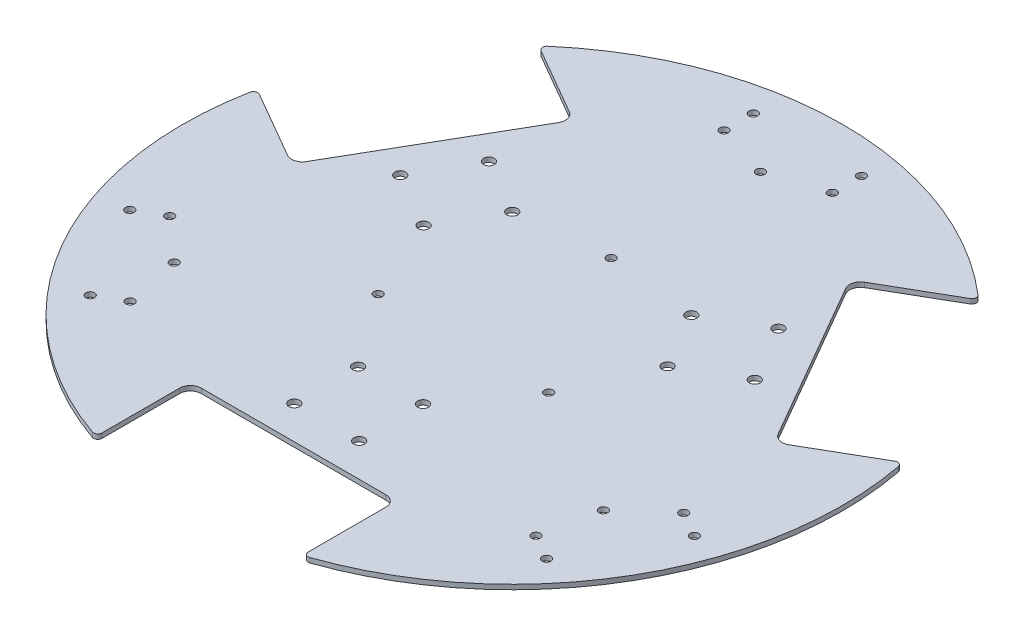
SolidWorks part; units mm, degrees
material "1060 Alloy"
ref_plane "Front Plane" through (0, 0, 0) normal (0, 0, 1) x (1, 0, 0)
ref_plane "Top Plane" through (0, 0, 0) normal (0, 1, 0) x (1, 0, 0)
ref_plane "Right Plane" through (0, 0, 0) normal (1, 0, 0) x (0, 0, -1)
sketch "Sketch1" plane through (0, 0, 0) normal (0, 1, 0) x (1, 0, 0)
  line L0 (0, -209.1984) -> (0, 195.424) construction
  line L1 (-47.65, -142.0744) -> (-47.65, -106.2645)
  line L2 (-42.65, -101.2645) -> (42.65, -101.2645)
  line L3 (47.65, -142.0744) -> (47.65, -106.2645)
  line L4 (-66.3726, 87.5682) -> (-109.0226, 13.6963)
  line L5 (-146.865, 29.7711) -> (-115.8528, 11.8661)
  line L6 (-99.215, 112.3033) -> (-68.2028, 94.3984)
  line L7 (109.0226, 13.6963) -> (66.3726, 87.5682)
  line L8 (99.215, 112.3033) -> (68.2028, 94.3984)
  line L9 (146.865, 29.7711) -> (115.8528, 11.8661)
  line L10 (170.2307, -98.2827) -> (-158.1389, 91.3016) construction
  line L11 (105.4743, -89.7631) -> (78.4297, -74.1489) construction
  line L12 (15, -56.4145) -> (15, -85.9145) construction
  arc A0 (50.3098, -143.9624) -> (149.83, 28.4116) centre (0, 0) ccw
  circle A1 centre (-15, -85.9145) radius 2.5
  circle A2 centre (15, -85.9145) radius 2.5
  circle A3 centre (105.4743, -89.7631) radius 2
  circle A4 centre (130.4743, -46.4619) radius 2
  circle A5 centre (93.783, -83.0131) radius 2
  circle A6 centre (118.783, -39.7119) radius 2
  circle A7 centre (99.1599, -57.25) radius 2
  circle A8 centre (39.4042, -22.75) radius 2
  circle A9 centre (-99.1599, -57.25) radius 2
  circle A10 centre (-93.783, -83.0131) radius 2
  circle A11 centre (-105.4743, -89.7631) radius 2
  circle A12 centre (-130.4743, -46.4619) radius 2
  circle A13 centre (-118.783, -39.7119) radius 2
  circle A14 centre (-39.4042, -22.75) radius 2
  circle A15 centre (0, 114.5) radius 2
  circle A16 centre (-25, 122.725) radius 2
  circle A17 centre (-25, 136.225) radius 2
  circle A18 centre (25, 136.225) radius 2
  circle A19 centre (25, 122.725) radius 2
  circle A20 centre (0, 45.5) radius 2
  arc A21 (-109.0226, 13.6963) -> (-115.8528, 11.8661) centre (-113.3528, 16.1963) cw
  arc A22 (-66.3726, 87.5682) -> (-68.2028, 94.3984) centre (-70.7028, 90.0682) ccw
  arc A23 (66.3726, 87.5682) -> (68.2028, 94.3984) centre (70.7028, 90.0682) cw
  arc A24 (109.0226, 13.6963) -> (115.8528, 11.8661) centre (113.3528, 16.1963) ccw
  arc A25 (47.65, -106.2645) -> (42.65, -101.2645) centre (42.65, -106.2645) ccw
  arc A26 (-47.65, -106.2645) -> (-42.65, -101.2645) centre (-42.65, -106.2645) cw
  arc A27 (99.5202, 115.5508) -> (-99.5202, 115.5508) centre (0, 0) ccw
  arc A28 (-149.83, 28.4116) -> (-50.3098, -143.9624) centre (0, 0) ccw
  arc A29 (-146.865, 29.7711) -> (-149.83, 28.4116) centre (-147.865, 28.039) ccw
  arc A30 (-99.215, 112.3033) -> (-99.5202, 115.5508) centre (-98.215, 114.0353) cw
  arc A31 (99.215, 112.3033) -> (99.5202, 115.5508) centre (98.215, 114.0353) ccw
  arc A32 (146.865, 29.7711) -> (149.83, 28.4116) centre (147.865, 28.039) cw
  arc A33 (47.65, -142.0744) -> (50.3098, -143.9624) centre (49.65, -142.0744) ccw
  arc A34 (-47.65, -142.0744) -> (-50.3098, -143.9624) centre (-49.65, -142.0744) cw
  circle A35 centre (15, -56.4145) radius 2.5
  circle A36 centre (-15, -56.4145) radius 2.5
  circle A37 centre (-56.3564, 15.2169) radius 2.5
  circle A38 centre (-81.9042, 29.9669) radius 2.5
  circle A39 centre (-66.9042, 55.9476) radius 2.5
  circle A40 centre (-41.3564, 41.1976) radius 2.5
  circle A41 centre (41.3564, 41.1976) radius 2.5
  circle A42 centre (66.9042, 55.9476) radius 2.5
  circle A43 centre (81.9042, 29.9669) radius 2.5
  circle A44 centre (56.3564, 15.2169) radius 2.5
  point P9 (0, -101.2645)
  point P20 (0, 0)
  point P65 (0, 0)
  point P73 (47.65, -101.2645)
  point P76 (-47.65, -101.2645)
  point P82 (101.6313, 113.6984)
  point P87 (47.65, -144.8645)
  point P90 (-47.65, -144.8645)
  point P113 (0, 0)
  dimension "D1" = 305
  dimension "D5" = 15.35
  dimension "D7" = 5
  dimension "D8" = 25
  dimension "D9" = 4
  dimension "D13" = 69
  dimension "D15" = 5
  dimension "D16" = 5
  dimension "D17" = 5
  dimension "D18" = 5
  dimension "D19" = 5
  dimension "D20" = 5
  dimension "D21" = 2
  dimension "D22" = 2
  dimension "D23" = 2
  dimension "D24" = 2
  dimension "D25" = 2
  dimension "D26" = 2
  dimension "D27" = 29.5
  dimension "D2" = 43.6
  dimension "D3" = 47.65
  dimension "D6" = 15
  dimension "D10" = 138.5
  dimension "D11" = 13.5
  dimension "D12" = 114.5
  dimension "D4" = 3
  dimension "D14" = 3
  dimension "D28" = 3
extrude "Boss-Extrude1" add sketch "Sketch1" along normal blind 2.2
